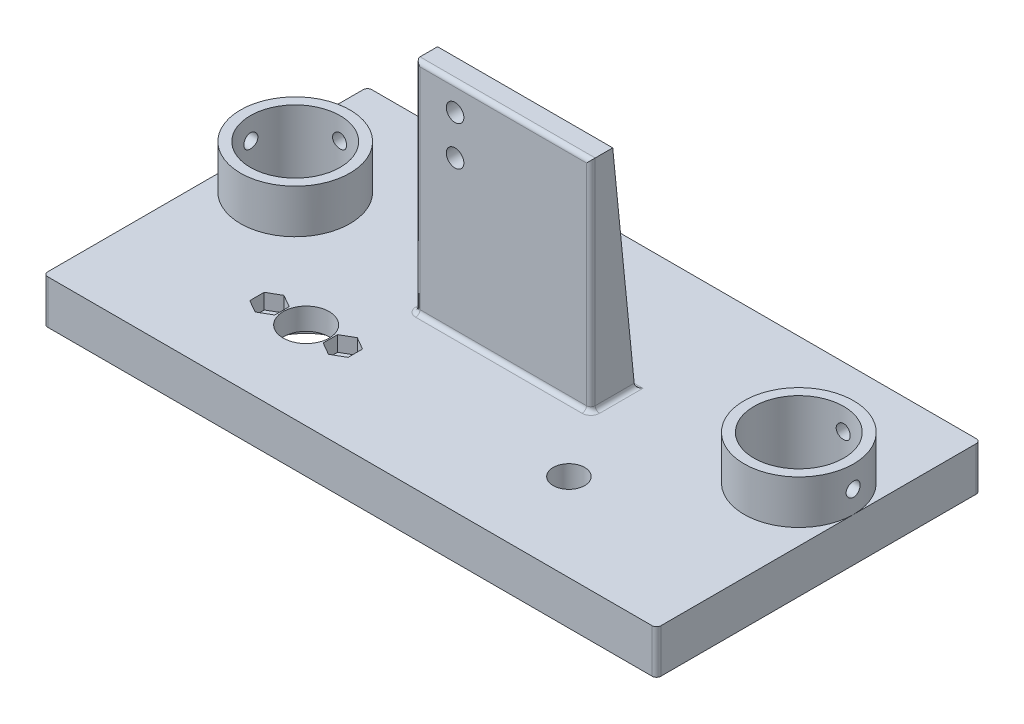
SolidWorks part; units mm, degrees
ref_plane "Alzado" through (0, 0, 0) normal (0, 0, 1) x (1, 0, 0)
ref_plane "Planta" through (0, 0, 0) normal (0, 1, 0) x (1, 0, 0)
ref_plane "Vista lateral" through (0, 0, 0) normal (1, 0, 0) x (0, 0, -1)
sketch "Croquis1" plane through (0, 0, 0) normal (0, 1, 0) x (1, 0, 0)
  line L0 (0, 0) -> (0, 31.359) construction
  line L1 (-45, -22.5) -> (45, -22.5)
  line L2 (-45, -22.5) -> (-45, 22.5)
  line L3 (-45, 22.5) -> (0, 22.5)
  line L4 (45, -22.5) -> (45, 22.5)
  line L5 (-45, -22.5) -> (45, 22.5) construction
  line L6 (-45, 22.5) -> (45, -22.5) construction
  line L11 (0, 22.5) -> (45, 22.5)
  point P0 (0, 0)
  dimension "D1" = 90
  dimension "D2" = 45
extrude "Saliente-Extruir1" add sketch "Croquis1" along normal blind 10
sketch "Croquis3" plane through (0, 10, 0) normal (0, 1, 0) x (1, 0, 0)
  line L0 (0, 0) -> (0, -3.5016) construction
  line L1 (-35.25, -2.5) -> (-41.5, -2.5) construction
  line L2 (-30, -2.5) -> (-30, 0.3209) construction
  line L3 (45, 22.5) -> (-45, 22.5) construction
  circle A0 centre (-30, -2.5) radius 5.25
  circle A1 centre (30, -2.5) radius 3.6
  circle A2 centre (-30, -2.5) radius 11.5 construction
  circle A3 centre (-38.375, -2.5) radius 1.6
  circle A4 centre (-21.625, -2.5) radius 1.6
  dimension "D1" = 10.5
  dimension "D2" = 7.2
  dimension "D4" = 23
  dimension "D5" = 3.2
  dimension "D3" = 60
  dimension "D6" = 25
extrude "Cortar-Extruir1" cut sketch "Croquis3" against normal through all
sketch "Croquis4" plane through (0, 10, 0) normal (0, 1, 0) x (1, 0, 0)
  line L0 (-21.625, -2.5) -> (-38.375, -2.5) construction
  line L1 (-38.375, 0.7909) -> (-41.225, -0.8546)
  line L2 (-41.225, -0.8546) -> (-41.225, -4.1454)
  line L3 (-41.225, -4.1454) -> (-38.375, -5.7909)
  line L4 (-38.375, -5.7909) -> (-35.525, -4.1454)
  line L5 (-35.525, -4.1454) -> (-35.525, -0.8546)
  line L6 (-35.525, -0.8546) -> (-38.375, 0.7909)
  line L7 (-21.625, 0.7909) -> (-24.475, -0.8546)
  line L8 (-24.475, -0.8546) -> (-24.475, -4.1454)
  line L9 (-24.475, -4.1454) -> (-21.625, -5.7909)
  line L10 (-21.625, -5.7909) -> (-18.775, -4.1454)
  line L11 (-18.775, -4.1454) -> (-18.775, -0.8546)
  line L12 (-18.775, -0.8546) -> (-21.625, 0.7909)
  circle A0 centre (-38.375, -2.5) radius 2.85 construction
  circle A1 centre (-21.625, -2.5) radius 2.85 construction
  dimension "D1" = 5.7
extrude "Cortar-Extruir2" cut sketch "Croquis4" against normal blind 3.5
sketch "Croquis5" plane through (0, 0, 0) normal (0, -1, 0) x (1, 0, 0)
  circle A0 centre (-30, 2.5) radius 11.75
  dimension "D1" = 23.5
extrude "Cortar-Extruir3" cut sketch "Croquis5" against normal blind 5
sketch "Croquis6" plane through (0, 10, 0) normal (0, 1, 0) x (1, 0, 0)
  line L0 (-45, -22.5) -> (45, -22.5) construction
  line L3 (-45, 22.5) -> (-45, -22.5) construction
  line L4 (45, -22.5) -> (45, 22.5) construction
  line L5 (0, 0) -> (0, 19.7465) construction
  line L11 (-45, -22.5) -> (45, -22.5)
  line L12 (-45, -22.5) -> (-45, -5.1795)
  line L13 (45, -22.5) -> (45, -5.1795)
  arc A0 (12.6923, -14.5059) -> (-12.6923, -14.5059) centre (0, -22.5) ccw
  arc A2 (12.6923, -14.5059) -> (45, -5.1795) centre (27.5, -5.1795) ccw
  arc A3 (-12.6923, -14.5059) -> (-45, -5.1795) centre (-27.5, -5.1795) cw
  line M22 (45, 22.5) -> (-45, 22.5)
  line M26 (45, 22.5) -> (-45, 22.5)
  line M27 (-45, 22.5) -> (-45, -22.5)
  line M28 (-45, -22.5) -> (45, -22.5)
  line M29 (45, -22.5) -> (45, 22.5)
  dimension "D1" = 30
  dimension "D2" = 17.5
extrude "Cortar-Extruir4" [suppressed] cut sketch "Croquis6" against normal through all contours A3 M28 M26 M27 | A0 A3 L11 A2 | A2 L11 M29 M22
sketch "Croquis8" plane through (0, 10, 0) normal (0, 1, 0) x (1, 0, 0)
  line L1 (45, 22.5) -> (-45, 22.5) construction
  line L2 (-44, 22.5) -> (44, 22.5) construction
  line L26 (0, 0) -> (0, 63.8128) construction
  line L31 (-45, 51.5) -> (45, 51.5)
  line L37 (-45, 22.5) -> (45, 22.5)
  line L46 (-45, 22.5) -> (-45, 51.5)
  line L50 (45, 22.5) -> (45, 51.5)
  dimension "D1" = 29
extrude "Saliente-Extruir2" add sketch "Croquis8" against normal blind 10
sketch "Croquis9" plane through (0, 0, 0) normal (0, 1, 0) x (1, 0, 0)
  line L0 (-45, 51.5) -> (-45, -22.5) construction
  line L1 (-45, 10) -> (-70, 10)
  line L2 (-45, 10) -> (-45, 35)
  line L3 (-45, 35) -> (-70, 35)
  line L4 (-70, 10) -> (-70, 35)
  line L5 (0, 0) -> (0, 51.5) construction
  line L12 (45, 35) -> (70, 35)
  line L13 (70, 10) -> (70, 35)
  line L14 (45, 10) -> (70, 10)
  line L15 (45, 10) -> (45, 35)
  dimension "D1" = 25
  dimension "D2" = 25
  dimension "D3" = 10
extrude "Saliente-Extruir4" add sketch "Croquis9" along normal blind 10
sketch "Croquis13" plane through (0, 10, 0) normal (0, 1, 0) x (1, 0, 0)
  line L0 (-45, 35) -> (-70, 10) construction
  line L1 (45, 10) -> (70, 35) construction
  line L2 (70, 10) -> (70, 35) construction
  line L3 (-70, 35) -> (-70, 10) construction
  circle A0 centre (-57.5, 22.5) radius 12.5
  circle A1 centre (57.5, 22.5) radius 12.5
extrude "Saliente-Extruir5" add sketch "Croquis13" along normal blind 10
sketch "Croquis15" plane through (0, 20, 0) normal (0, 1, 0) x (1, 0, 0)
  line L1 (0, 0) -> (0, 22.5) construction
  line L2 (-44, 22.5) -> (44, 22.5) construction
  circle A0 centre (-57.5, 22.5) radius 10.25
  circle A1 centre (57.5, 22.5) radius 10.25
  dimension "D1" = 20.5
extrude "Cortar-Extruir5" cut sketch "Croquis15" against normal blind 20
sketch "Croquis16" plane through (0, 0, -35) normal (0, 0, -1) x (-1, 0, 0)
  line L0 (-57.5, 20) -> (-57.5, 10) construction
  line L1 (-45, 20) -> (-70, 20) construction
  line L2 (57.5, 20) -> (57.5, 10) construction
  line L3 (70, 20) -> (45, 20) construction
  circle A0 centre (-57.5, 15) radius 1.6
  circle A1 centre (57.5, 15) radius 1.6
  dimension "D1" = 3.2
extrude "Cortar-Extruir6" cut sketch "Croquis16" against normal blind 10
sketch "Croquis17" plane through (0, 0, 0) normal (0, 1, 0) x (1, 0, 0)
  line L0 (-45, 51.5) -> (45, 51.5) construction
  line L9 (45, 51.5) -> (70, 51.5)
  line L10 (45, 51.5) -> (45, 35)
  line L11 (45, 35) -> (70, 35)
  line L12 (70, 51.5) -> (70, 35)
  line L13 (70, 10) -> (45, 10)
  line L14 (70, 10) -> (70, -22.5)
  line L15 (70, -22.5) -> (45, -22.5)
  line L16 (45, 10) -> (45, -22.5)
  line L17 (-70, 35) -> (-45, 35)
  line L18 (-70, 35) -> (-70, 51.5)
  line L19 (-70, 51.5) -> (-45, 51.5)
  line L20 (-45, 35) -> (-45, 51.5)
  line L21 (-70, 10) -> (-45, 10)
  line L22 (-70, 10) -> (-70, -22.5)
  line L23 (-70, -22.5) -> (-45, -22.5)
  line L24 (-45, 10) -> (-45, -22.5)
  point P4 (0, 0)
  point P27 (0, 0)
extrude "Saliente-Extruir6" add sketch "Croquis17" along normal blind 10
sketch "Croquis19" plane through (0, 0, 0) normal (1, 0, 0) x (0, 0, -1)
  line L0 (22.5, 20) -> (22.5, 10) construction
  line L1 (35, 20) -> (10, 20) construction
  circle A0 centre (22.5, 15) radius 1.6
  dimension "D1" = 3.2
extrude "Cortar-Extruir10" cut sketch "Croquis19" along normal through all from offset 60
mirror "Simetría1" about plane through (0, 0, 0) normal (1, 0, 0) of "Cortar-Extruir10"
sketch "Croquis20" plane through (0, 10, 0) normal (0, 1, 0) x (1, 0, 0)
  line L0 (-45, 22.5) -> (45, 22.5) construction
  line L1 (-20, 22.5) -> (-17, 22.5)
  line L2 (-20, 22.5) -> (-20, 12.5)
  line L3 (-20, 12.5) -> (20, 12.5)
  line L4 (20, 22.5) -> (20, 12.5)
  line L5 (0, 0) -> (0, 63.8128) construction
  line L6 (0, 0) -> (0, 63.8128) construction
  line L7 (17, 22.5) -> (17, 17.5)
  line L8 (17, 17.5) -> (-17, 17.5)
  line L9 (-17, 17.5) -> (-17, 22.5)
  line L10 (17, 22.5) -> (20, 22.5)
  dimension "D1" = 10
  dimension "D2" = 40
  dimension "D3" = 3
  dimension "D4" = 5
extrude "Saliente-Extruir7" add sketch "Croquis20" along normal blind 50
sketch "Croquis21" plane through (0, 0, -12.5) normal (0, 0, 1) x (1, 0, 0)
  line L0 (0, 60) -> (0, 40.6146) construction
  line L1 (-20, 60) -> (20, 60) construction
  line L3 (-14, 60) -> (14, 60) construction
  line L4 (-14, 60) -> (-14, 20) construction
  line L5 (-14, 20) -> (14, 20) construction
  line L6 (14, 60) -> (14, 20) construction
  circle A0 centre (-11, 54) radius 2
  circle A1 centre (-11, 45) radius 2
  point P9 (0, 60)
  point P14 (0, 0)
  dimension "D3" = 4
  dimension "D1" = 28
  dimension "D2" = 40
  dimension "D4" = 3
  dimension "D5" = 9
  dimension "D6" = 6
extrude "Cortar-Extruir11" cut sketch "Croquis21" against normal through all
sketch "Croquis22" plane through (20, 0, 0) normal (1, 0, 0) x (0, 0, -1)
  line L0 (17.5, 60) -> (22.5, 10)
  line L1 (17.5, 60) -> (22.5, 60)
  line L2 (22.5, 60) -> (22.5, 10)
extrude "Cortar-Extruir12" cut sketch "Croquis22" against normal up to surface (40 mm away) up to face at (-20, 35, -17.5)
fillet "Redondeo2" radius 1 4 edges at (-70, 5, 22.5) (-70, 5, -51.5) (70, 5, 22.5) (70, 5, -51.5)
fillet "Redondeo3" radius 1 13 edges at (-20, 35, -12.5) (0, 60, -12.5) (20, 35, -12.5) (0, 10, -12.5) (17, 35, -17.5) (-17, 35, -17.5) (20, 10, -17.5) (18.5, 10, -22.5) (17, 10, -20) (0, 10, -17.5) (-17, 10, -20) (-18.5, 10, -22.5) (-20, 10, -17.5)
